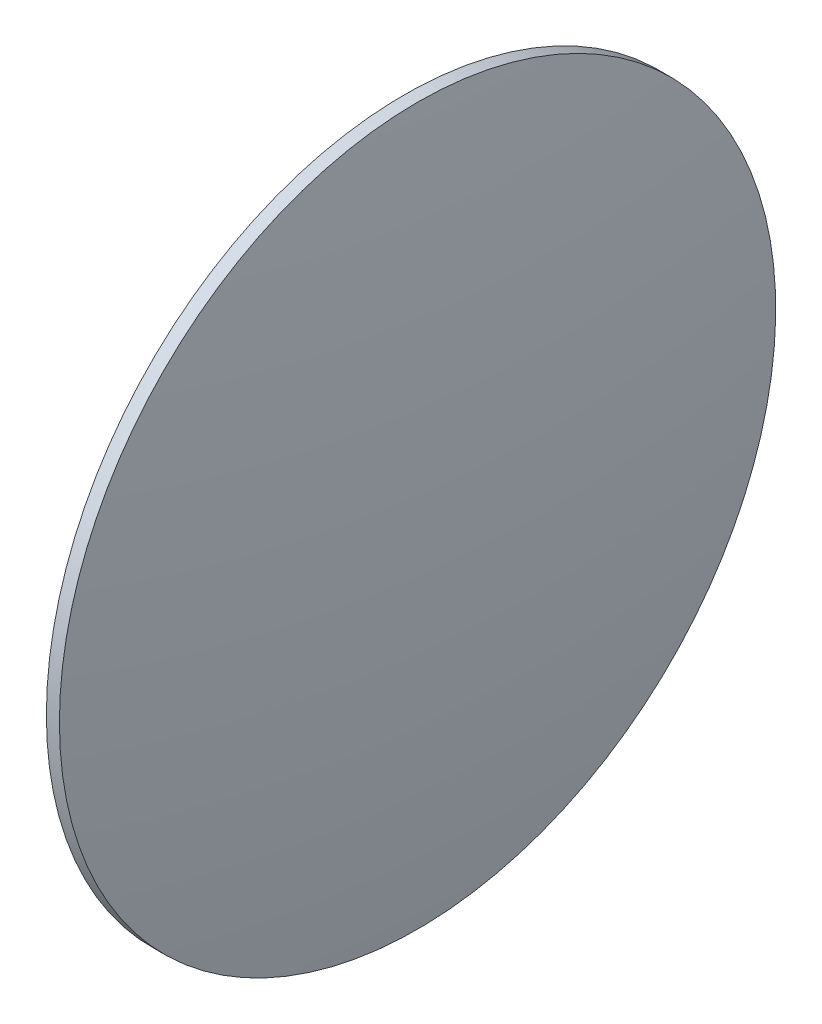
SolidWorks part; units mm, degrees
ref_plane "Front" through (0, 0, 0) normal (0, 0, 1) x (1, 0, 0)
ref_plane "Top" through (0, 0, 0) normal (0, 1, 0) x (1, 0, 0)
ref_plane "Right" through (0, 0, 0) normal (1, 0, 0) x (0, 0, -1)
sketch "Sketch1" plane through (0, 0, 0) normal (0, 0, 1) x (1, 0, 0)
  line L0 (-100, 0) -> (100, 0)
  line L1 (0, 27.476) -> (0, -27.476)
  point P5 (0, 0)
  point P6 (-50, 0)
  point P7 (50, 0)
  dimension "D1" = 200
  dimension "D2" = 50
  dimension "D3" = 50
sketch "Sketch3" plane through (0, 0, 0) normal (0, 0, 1) x (1, 0, 0)
  line L0 (0, 27.476) -> (1, 27.476)
  line L1 (0, 0) -> (2.8963, 0)
  line L2 (-100, 0) -> (100, 0) construction
  line L3 (0, 27.476) -> (0, 0)
  arc A0 (1, 27.476) -> (2.8963, 0) centre (-197.1037, 0) cw
  dimension "D2" = 200
  dimension "D1" = 1
revolve "Revolve1" add sketch "Sketch3" angle 360 about L0
